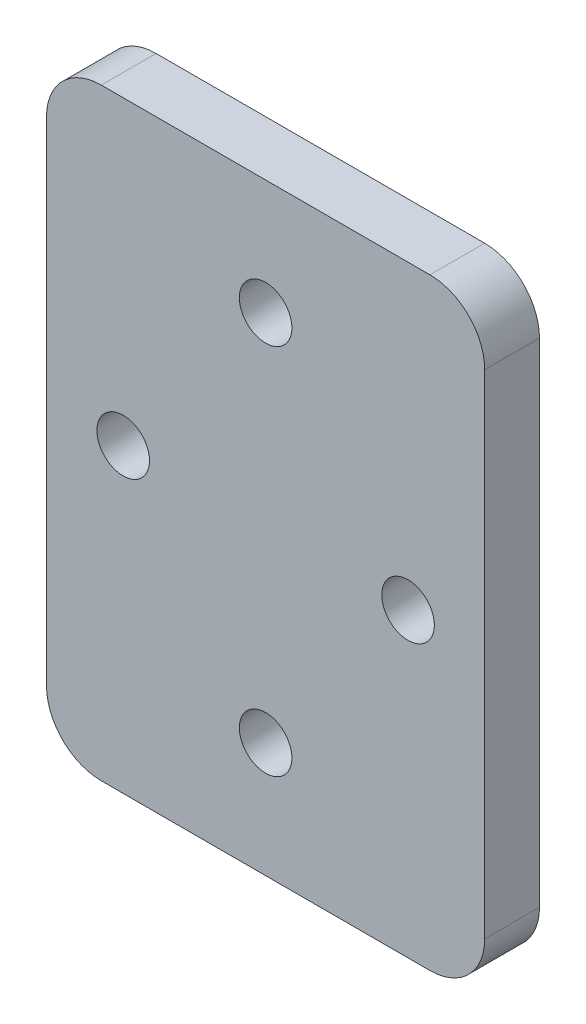
SolidWorks part; units mm, degrees
ref_plane "Front Plane" through (0, 0, 0) normal (0, 0, 1) x (1, 0, 0)
ref_plane "Top Plane" through (0, 0, 0) normal (0, 1, 0) x (1, 0, 0)
ref_plane "Right Plane" through (0, 0, 0) normal (1, 0, 0) x (0, 0, -1)
sketch "Sketch1" plane through (0, 0, 0) normal (0, 0, 1) x (1, 0, 0)
  line L1 (-20, 27.5) -> (20, 27.5)
  line L2 (-20, 27.5) -> (-20, -27.5)
  line L3 (-20, -27.5) -> (20, -27.5)
  line L4 (20, 27.5) -> (20, -27.5)
  line L5 (0, -27.5) -> (0, 27.5) construction
  line L6 (-20, 0) -> (20, 0) construction
  circle A0 centre (0, 17) radius 2.4
  circle A1 centre (-13, 0) radius 2.4
  circle A2 centre (0, -17) radius 2.4
  circle A3 centre (13, 0) radius 2.4
  point P0 (0, 0)
  dimension "D3" = 4.8
  dimension "D5" = 4.8
  dimension "D1" = 55
  dimension "D2" = 40
  dimension "D4" = 17
  dimension "D6" = 13
extrude "Boss-Extrude1" add sketch "Sketch1" along normal blind 5
fillet "Fillet1" radius 5 4 edges at (20, 27.5, 2.5) (20, -27.5, 2.5) (-20, -27.5, 2.5) (-20, 27.5, 2.5)
